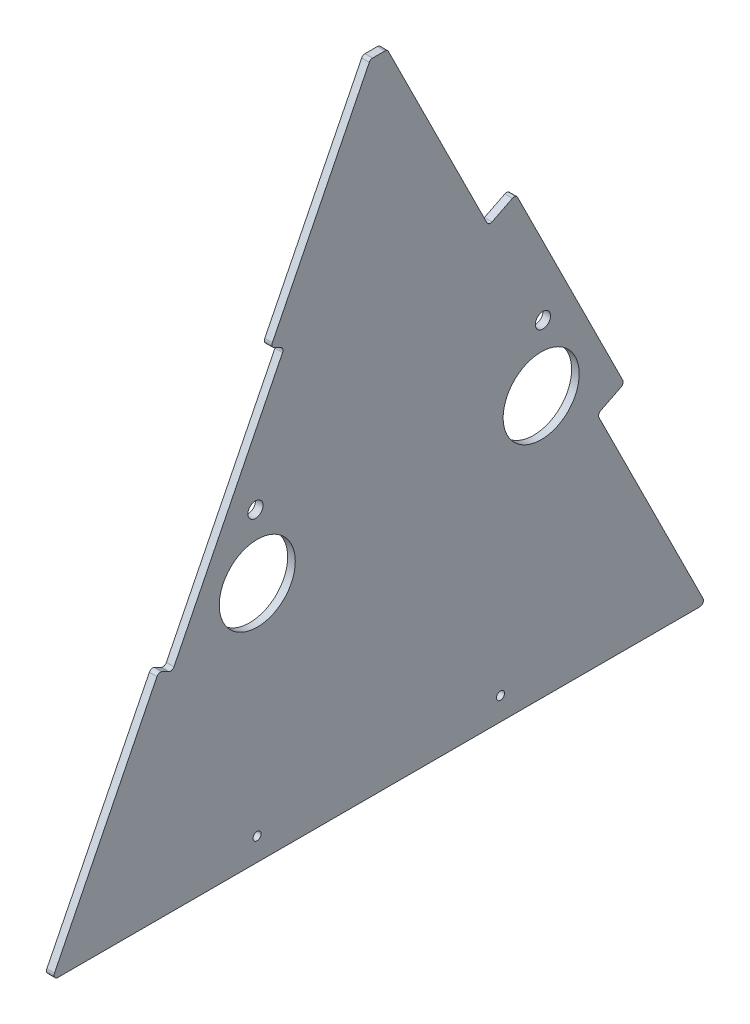
SolidWorks part; units mm, degrees
material "PC High Viscosity"
ref_plane "Front Plane" through (0, 0, 0) normal (0, 0, 1) x (1, 0, 0)
ref_plane "Top Plane" through (0, 0, 0) normal (0, 1, 0) x (1, 0, 0)
ref_plane "Right Plane" through (0, 0, 0) normal (1, 0, 0) x (0, 0, -1)
sketch "Sketch1" plane through (0, 0, 0) normal (1, 0, 0) x (0, 0, -1)
  line L0 (171.45, 19.05) -> (374.65, 19.05) construction
  line L1 (0, 0) -> (546.1, 0)
  line L5 (0, 0) -> (89.2507, 179.0092)
  line L11 (265.9434, 533.4) -> (280.1566, 533.4)
  line L12 (280.1566, 533.4) -> (364.7652, 363.7013)
  line L13 (364.7652, 363.7013) -> (387.4965, 375.0347)
  line L14 (387.4965, 375.0347) -> (478.1639, 193.1841)
  line L15 (478.1639, 193.1841) -> (455.4326, 181.8507)
  line L16 (182.7515, 366.5427) -> (194.1171, 360.876)
  line L17 (194.1171, 360.876) -> (100.6164, 173.3425)
  line L18 (100.6164, 173.3425) -> (89.2507, 179.0092)
  line L19 (455.4326, 181.8507) -> (546.1, 0)
  line L20 (182.7515, 366.5427) -> (265.9434, 533.4)
  circle A0 centre (171.45, 19.05) radius 3.3734
  circle A1 centre (374.65, 19.05) radius 3.3734
  circle A7 centre (410.0989, 272.776) radius 6.35
  circle A8 centre (170.0981, 255.7759) radius 6.35
  circle A9 centre (171.5793, 201.8212) radius 31.75
  circle A10 centre (408.6177, 218.8213) radius 31.75
  point P2 (273.05, 533.4)
  point P9 (273.05, 19.05)
  point P10 (273.05, 0)
  dimension "D4" = 6.7469
  dimension "D7" = 25.4
  dimension "D11" = 209.55
  dimension "D20" = 12.7
  dimension "D21" = 63.5
  dimension "D25" = 50.8
  dimension "D1" = 546.1
  dimension "D2" = 63.5
  dimension "D3" = 203.2
  dimension "D5" = 19.05
  dimension "D6" = 533.4
  dimension "D8" = 203.2
  dimension "D9" = 203.2
  dimension "D10" = 200.025
  dimension "D12" = 12.7
  dimension "D16" = 104.775
  dimension "D17" = 101.6
  dimension "D18" = 25.4
  dimension "D19" = 25.4
  dimension "D22" = 50.8
  dimension "D23" = 57.15
  dimension "D24" = 53.975
extrude "Boss-Extrude1" add sketch "Sketch1" along normal blind 6.35
fillet "Fillet1" radius 3.175 12 edges at (3.175, 533.4, -280.1566) (3.175, 0, 0) (3.175, 179.0092, -89.2507) (3.175, 173.3425, -100.6164) (3.175, 360.876, -194.1171) (3.175, 366.5427, -182.7515) (3.175, 533.4, -265.9434) (3.175, 363.7013, -364.7652) (3.175, 375.0347, -387.4965) (3.175, 193.1841, -478.1639) (3.175, 181.8507, -455.4326) (3.175, 0, -546.1)
